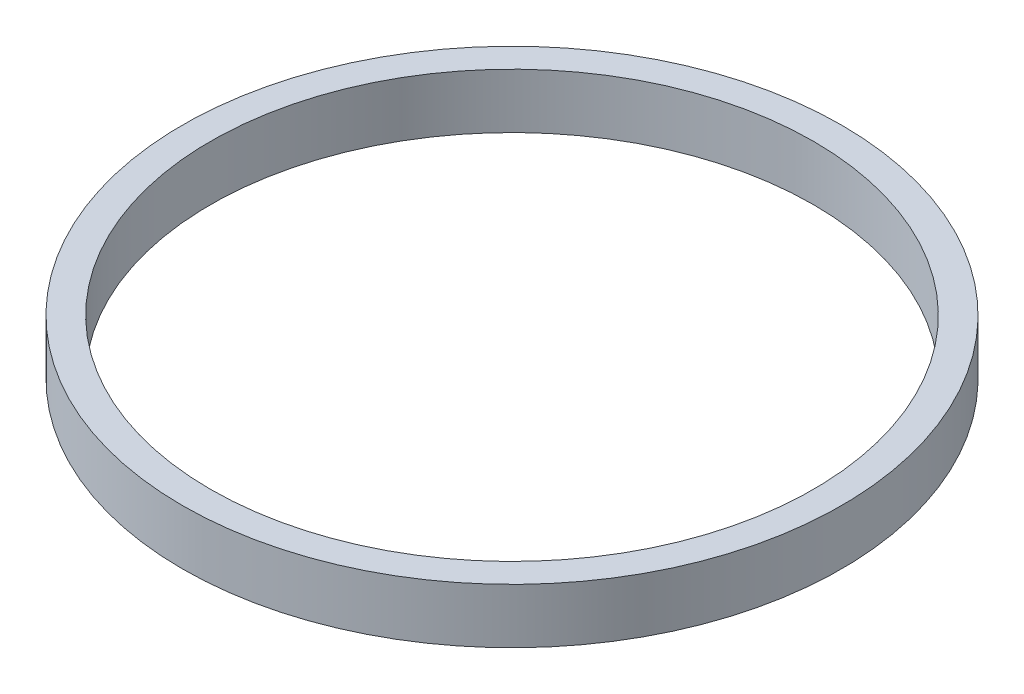
SolidWorks part; units mm, degrees
ref_plane "Front Plane" through (0, 0, 0) normal (0, 0, 1) x (1, 0, 0)
ref_plane "Top Plane" through (0, 0, 0) normal (0, 1, 0) x (1, 0, 0)
ref_plane "Right Plane" through (0, 0, 0) normal (1, 0, 0) x (0, 0, -1)
sketch "Sketch1" plane through (0, 0, 0) normal (0, 1, 0) x (1, 0, 0)
  circle A0 centre (0, 0) radius 76.25
  circle A1 centre (0, 0) radius 69.75
  dimension "D1" = 152.5
  dimension "D2" = 6.5
extrude "Boss-Extrude1" add sketch "Sketch1" along normal blind 12.7
